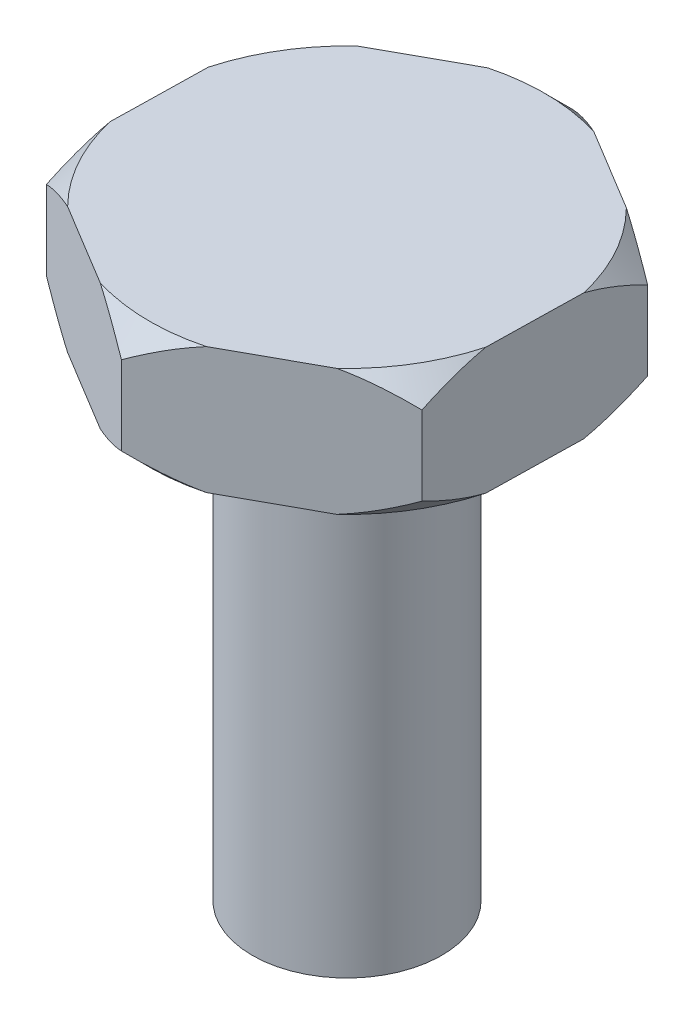
SolidWorks part; units mm, degrees
ref_plane "Ebene vorne" through (0, 0, 0) normal (0, 0, 1) x (1, 0, 0)
ref_plane "Ebene oben" through (0, 0, 0) normal (0, 1, 0) x (1, 0, 0)
ref_plane "Ebene rechts" through (0, 0, 0) normal (1, 0, 0) x (0, 0, -1)
sketch "Sketch1" plane through (0, 0, 0) normal (0, 0, 1) x (1, 0, 0)
  line L0 (0, 26.2734) -> (0, -23.1797) construction
  line L1 (0, 0) -> (-3, 0)
  line L2 (-3, 0) -> (-3, 15)
  line L3 (-3, 15) -> (-7, 15)
  line L4 (-7, 15) -> (-7, 19)
  line L5 (-7, 19) -> (0, 19)
  line L6 (0, 0) -> (0, 19)
  dimension "D1" = 3
  dimension "D2" = 4
  dimension "D3" = 15
  dimension "D4" = 4
revolve "Revolve1" add sketch "Sketch1" angle 360 about L0
chamfer "Chamfer1" distance 0.75 angle 45 2 edges at (0, 15, 7) (0, 19, 7)
sketch "Sketch2" plane through (0, 19, 0) normal (0, 1, 0) x (1, 0, 0)
  line L1 (0.1388, 6.9986) -> (-5.9916, 3.6195)
  line L2 (-5.9916, 3.6195) -> (-6.1304, -3.3791)
  line L3 (-6.1304, -3.3791) -> (-0.1388, -6.9986)
  line L4 (-0.1388, -6.9986) -> (5.9916, -3.6195)
  line L5 (5.9916, -3.6195) -> (6.1304, 3.3791)
  line L6 (6.1304, 3.3791) -> (0.1388, 6.9986)
  circle A0 centre (0, 0) radius 6.0622 construction
  circle A1 centre (0, 0) radius 7 construction
extrude "Cut-Extrude1" cut sketch "Sketch2" against normal blind 10 flip side to cut
